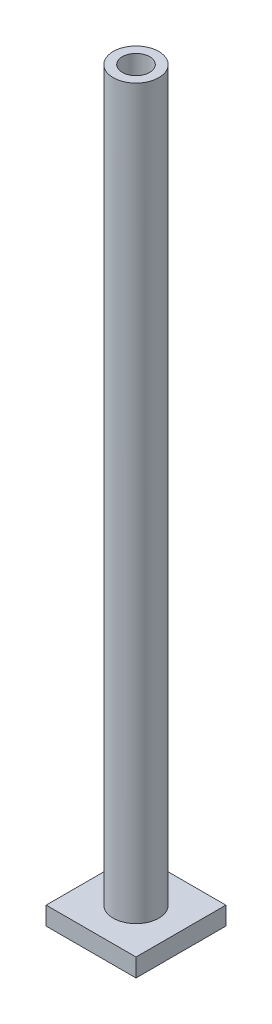
SolidWorks part; units mm, degrees
ref_plane "Front Plane" through (0, 0, 0) normal (0, 0, 1) x (1, 0, 0)
ref_plane "Top Plane" through (0, 0, 0) normal (0, 1, 0) x (1, 0, 0)
ref_plane "Right Plane" through (0, 0, 0) normal (1, 0, 0) x (0, 0, -1)
sketch "Sketch1" plane through (0, 0, 0) normal (0, 1, 0) x (1, 0, 0)
  line L1 (7.9, 7.9) -> (-7.9, 7.9)
  line L2 (7.9, 7.9) -> (7.9, -7.9)
  line L3 (7.9, -7.9) -> (-7.9, -7.9)
  line L4 (-7.9, 7.9) -> (-7.9, -7.9)
  line L5 (7.9, 7.9) -> (-7.9, -7.9) construction
  line L6 (7.9, -7.9) -> (-7.9, 7.9) construction
  point P0 (0, 0)
  dimension "D1" = 15.8
extrude "Base" add sketch "Sketch1" along normal blind 3.2
sketch "Sketch2" plane through (0, 0, 0) normal (0, -1, 0) x (1, 0, 0)
  line L0 (0, 6.6) -> (0, -6.6) construction
  line L1 (6.6, 6.6) -> (-6.6, 6.6)
  line L2 (6.6, 6.6) -> (6.6, -6.6)
  line L3 (6.6, -6.6) -> (-6.6, -6.6)
  line L4 (-6.6, 6.6) -> (-6.6, -6.6)
  line L5 (6.6, 6.6) -> (-6.6, -6.6) construction
  line L6 (6.6, -6.6) -> (-6.6, 6.6) construction
  line L7 (-6.6, 0) -> (6.6, 0) construction
  line L8 (-7.9, -7.9) -> (-7.9, 7.9) construction
  line L9 (0, -6.6) -> (0, -7.9) construction
  line L10 (7.9, -7.9) -> (-7.9, -7.9) construction
  line L12 (-1.25, -6.6) -> (1.25, -6.6)
  line L13 (-1.25, -6.6) -> (-1.25, -7.9)
  line L14 (-1.25, -7.9) -> (1.25, -7.9)
  line L15 (1.25, -6.6) -> (1.25, -7.9)
  line L16 (-1.25, -6.6) -> (1.25, -7.9) construction
  line L17 (-1.25, -7.9) -> (1.25, -6.6) construction
  line L18 (-1.25, -2.1651) -> (1.25, -2.1651)
  line L19 (-1.25, -2.1651) -> (-1.25, -6.6)
  line L20 (-1.25, -6.6) -> (1.25, -6.6)
  line L21 (1.25, -2.1651) -> (1.25, -6.6)
  circle A4 centre (0, 0) radius 3.4
  circle A5 centre (0, 0) radius 2.5
  point P0 (0, 0)
  point P6 (0, -7.25)
  dimension "D4" = 5
  dimension "D2" = 1.3
  dimension "D5" = 0.9
  dimension "D1" = 2.5
extrude "Bottom cut" cut sketch "Sketch2" against normal offset from surface (2 mm away) 1.2 contours A4 L21 L3 L2 L1 L4 L19 | L18 A5 | L18 A5 | A4 L19 L3 L21 up to face at (0, 3.2, 0)
sketch "Sketch3" plane through (0, 3.2, 0) normal (0, 1, 0) x (1, 0, 0)
  circle A0 centre (0, 0) radius 4
  circle A1 centre (0, 0) radius 2.4
  dimension "D1" = 8
  dimension "D2" = 1.6
extrude "Lamp post" add sketch "Sketch3" along normal blind 128
sketch "Sketch4" plane through (0, 3.2, 0) normal (0, 1, 0) x (1, 0, 0)
  circle A0 centre (0, 0) radius 2.4 construction
  circle A1 centre (0, 0) radius 2.4
extrude "Wire bottom cut" cut sketch "Sketch4" against normal up to next
equation "\"P\"= \"LegoUnit\" * 5"
equation "\"D1@Sketch1\" = \"BrickSize\" * 2 - \"Padding\""
equation "\"Padding\"= \"LegoUnit\" / 8"
equation "\"SmallHeight\"= \"LegoUnit\" * 2"
equation "\"LargeHight\"= \"LegoUnit\" * 6"
equation "\"D1@Base\" = \"SmallHeight\""
equation "\"InsetDiameter\"= \"LegoUnit\" * 2 - \"Padding\" * 3"
equation "\"LegoUnit\"=1.6"
equation "\"BrickSize\"= \"LegoUnit\" * 5"
equation "\"WallSize\"= \"LegoUnit\" - \"Padding\" * 1.5"
equation "\"D2@Sketch2\"=\"WallSize\""
equation "\"BumpSize\"= \"LegoUnit\" * 3"
equation "\"InsideBumpSize\"= \"BumpSize\" + \"Padding\""
equation "\"InnerWallSize\"= \"Padding\" * 4.5"
equation "\"D5@Sketch2\"=\"InnerWallSize\""
equation "\"CeilingSize\"= \"LegoUnit\" - \"Padding\" * 2"
equation "\"D1@Bottom cut\" = \"CeilingSize\""
equation "\"D4@Sketch2\"=\"InsideBumpSize\""
equation "\"D1@Sketch3\"=\"BrickSize\""
equation "\"D2@Sketch3\"=\"LegoUnit\""
equation "\"D1@Lamp post\"=\"SmallHeight\" * 40"
